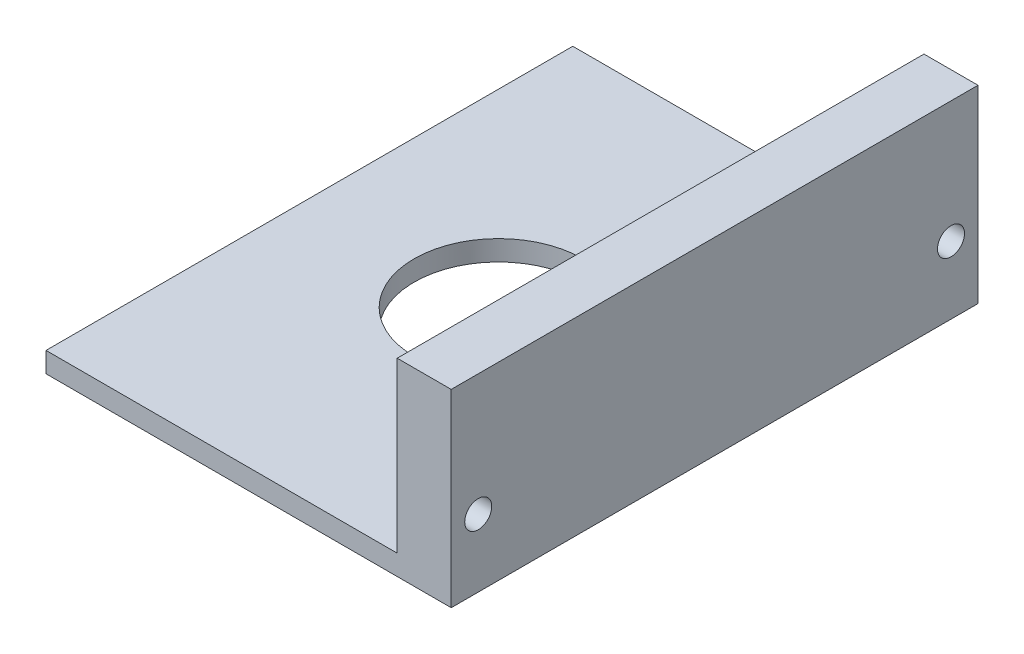
SolidWorks part; units mm, degrees
material "6061 Alloy"
ref_plane "Front Plane" through (0, 0, 0) normal (0, 0, 1) x (1, 0, 0)
ref_plane "Top Plane" through (0, 0, 0) normal (0, 1, 0) x (1, 0, 0)
ref_plane "Right Plane" through (0, 0, 0) normal (1, 0, 0) x (0, 0, -1)
sketch "Sketch1" plane through (0, 0, 0) normal (0, 1, 0) x (1, 0, 0)
  line L1 (-30, 39) -> (30, 39)
  line L2 (-30, 39) -> (-30, -39)
  line L3 (-30, -39) -> (30, -39)
  line L4 (30, 39) -> (30, -39)
  line L5 (-30, 39) -> (30, -39) construction
  line L6 (-30, -39) -> (30, 39) construction
  point P0 (0, 0)
  dimension "D1" = 60
extrude "Boss-Extrude1" add sketch "Sketch1" along normal blind 3
sketch "Sketch2" plane through (0, 3, 0) normal (0, 1, 0) x (1, 0, 0)
  line L0 (22, -39) -> (22, 39)
  line L1 (-30, -39) -> (30, -39) construction
  line L2 (30, 39) -> (-30, 39) construction
  line L8 (30, -39) -> (30, 39)
  line L9 (30, 39) -> (-30, 39)
  line L10 (-30, 39) -> (-30, -39)
  line L11 (-30, -39) -> (30, -39)
  line L12 (30, -39) -> (30, 39)
  line L13 (30, 39) -> (22, 39)
  line L15 (22, -39) -> (30, -39)
  dimension "D1" = 0
extrude "Boss-Extrude2" add sketch "Sketch2" along normal blind 25
sketch "Sketch5" plane through (22, 0, 0) normal (-1, 0, 0) x (0, 0, 1)
  line L0 (39, 28) -> (39, 3) construction
  line L1 (-39, 28) -> (-39, 3) construction
  line L2 (-39, 3) -> (39, 3) construction
  circle A0 centre (35, 10) radius 2
  circle A1 centre (-35, 10) radius 2
  dimension "D1" = 4
  dimension "D2" = 4
  dimension "D3" = 7
  dimension "D4" = 7
extrude "Cut-Extrude2" cut sketch "Sketch5" against normal blind 30
sketch "Sketch6" plane through (0, 0, 0) normal (0, -1, 0) x (-1, 0, 0)
  line L0 (-30, -39) -> (-30, 39) construction
  circle A0 centre (2, 0) radius 12.5
  dimension "D1" = 25
  dimension "D2" = 32
extrude "Cut-Extrude3" cut sketch "Sketch6" against normal through all
